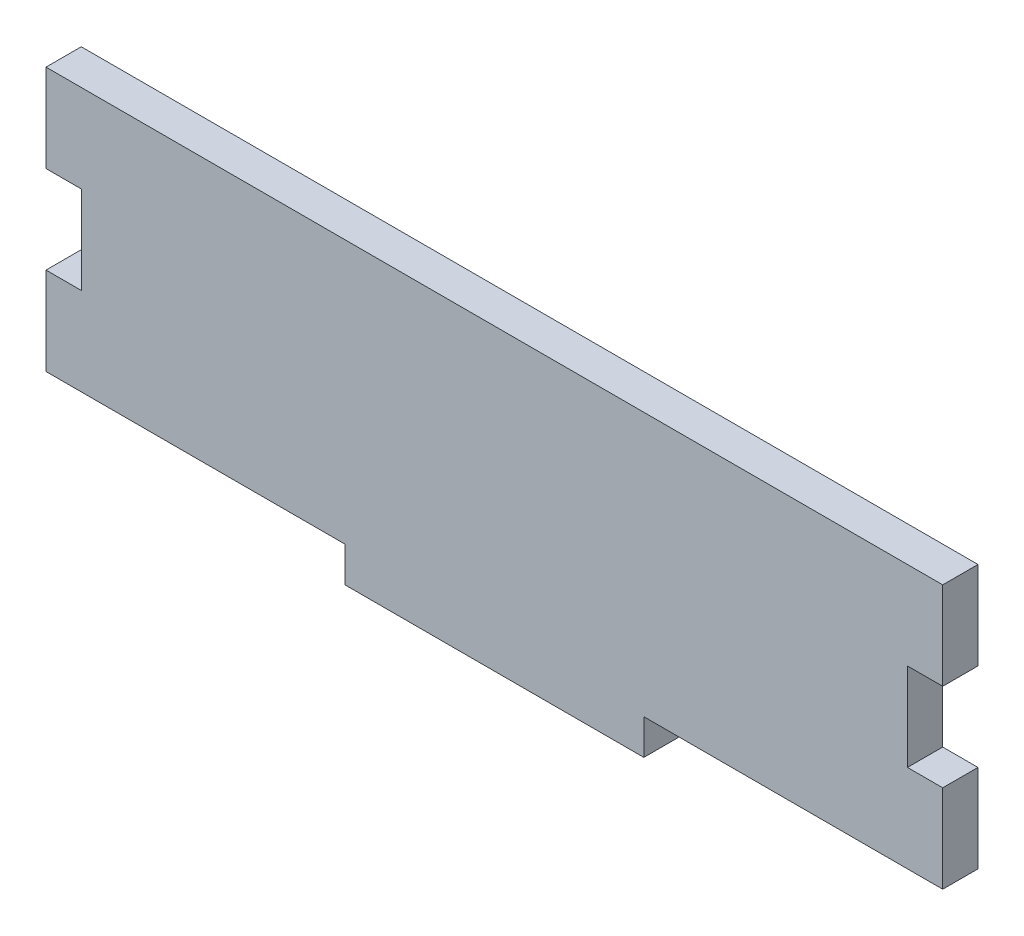
SolidWorks part; units mm, degrees
ref_plane "Front Plane" through (0, 0, 0) normal (0, 0, 1) x (1, 0, 0)
ref_plane "Top Plane" through (0, 0, 0) normal (0, 1, 0) x (1, 0, 0)
ref_plane "Right Plane" through (0, 0, 0) normal (1, 0, 0) x (0, 0, -1)
sketch "Sketch1" plane through (0, 0, 0) normal (0, 0, 1) x (1, 0, 0)
  line L0 (32.0492, 27.3312) -> (62.5292, 27.3312)
  line L1 (11.7292, 1.9312) -> (37.1292, 1.9312)
  line L2 (-13.6708, 4.9284) -> (-13.6708, 12.396)
  line L3 (-13.6708, 27.3312) -> (16.8092, 27.3312)
  line L4 (62.5292, 4.9284) -> (62.5292, 12.396)
  line L5 (-13.6708, 19.8636) -> (-13.6708, 27.3312)
  line L7 (-13.6708, 4.9284) -> (11.7292, 4.9284)
  line L8 (11.7292, 1.9312) -> (11.7292, 4.9284)
  line L11 (62.5292, 4.9284) -> (37.1292, 4.9284)
  line L12 (37.1292, 1.9312) -> (37.1292, 4.9284)
  line L13 (-13.6708, 19.8636) -> (-10.6736, 19.8636)
  line L14 (62.5292, 19.8636) -> (62.5292, 27.3312)
  line L15 (-13.6708, 12.396) -> (-10.6736, 12.396)
  line L16 (-10.6736, 19.8636) -> (-10.6736, 12.396)
  line L17 (62.5292, 19.8636) -> (59.532, 19.8636)
  line L18 (16.8092, 27.3312) -> (32.0492, 27.3312)
  line L19 (62.5292, 12.396) -> (59.532, 12.396)
  line L20 (59.532, 19.8636) -> (59.532, 12.396)
  dimension "width" = 76.2
  dimension "height" = 25.4
  dimension "thick" = 2.9972
extrude "Boss-Extrude1" add sketch "Sketch1" along normal blind 2.9972
